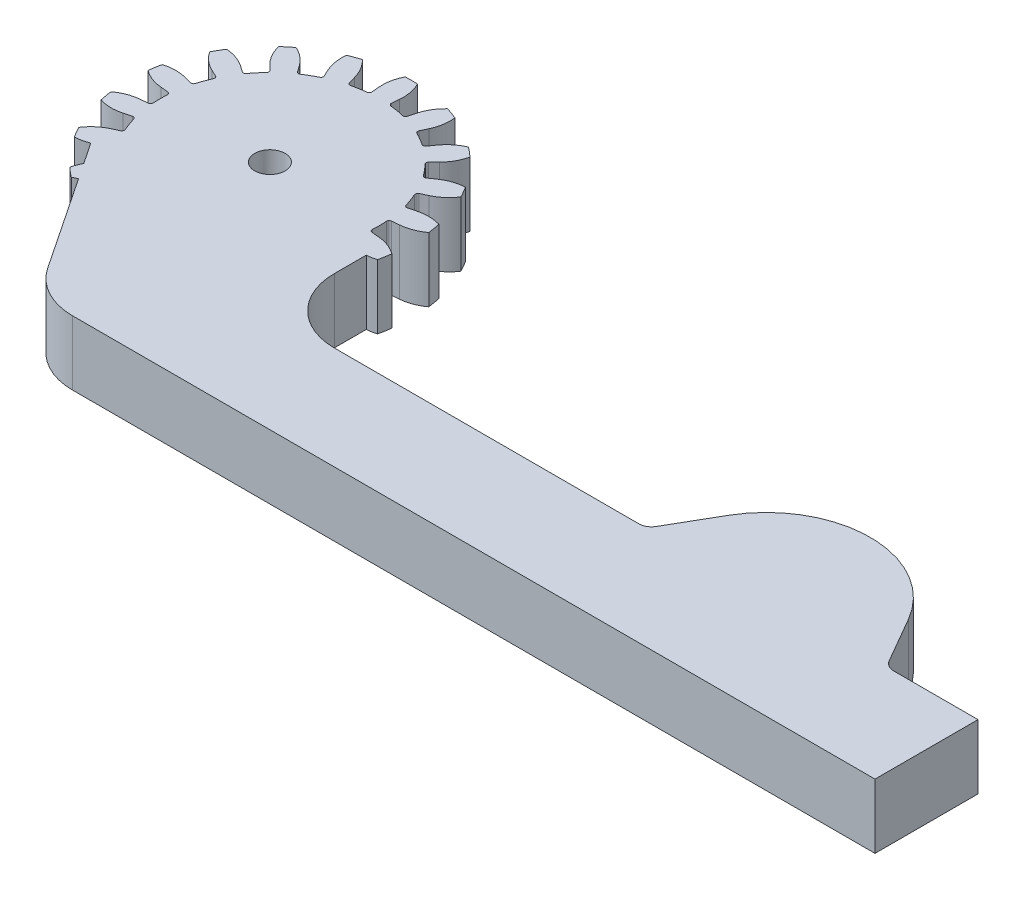
SolidWorks part; units mm, degrees
ref_plane "Front Plane" through (0, 0, 0) normal (0, 0, 1) x (1, 0, 0)
ref_plane "Top Plane" through (0, 0, 0) normal (0, 1, 0) x (1, 0, 0)
ref_plane "Right Plane" through (0, 0, 0) normal (1, 0, 0) x (0, 0, -1)
sketch "Sketch1" plane through (0, 0, 0) normal (0, 1, 0) x (1, 0, 0)
  line L0 (0, 0) -> (0, 13.97) construction
  line L1 (0, 0) -> (-0.6094, 13.9567) construction
  line L2 (0, 0) -> (-1.0297, 11.7695) construction
  line L3 (0, 0) -> (-1.88, 10.6623) construction
  line L4 (0, 0) -> (-1.88, 10.6623)
  line L5 (-0.9655, 11.0357) -> (-1.0297, 11.7695)
  line L6 (0, 0) -> (1.88, 10.6623)
  line L7 (0.9655, 11.0357) -> (1.0297, 11.7695)
  circle A0 centre (0, 0) radius 13.97 construction
  circle A1 centre (0, 0) radius 11.8144 construction
  circle A2 centre (0, 0) radius 10.8268 construction
  arc A3 (-1.88, 10.6623) -> (-1.1906, 10.7611) centre (0, 0) cw
  arc A4 (-1.0297, 11.7695) -> (-0.6094, 13.9567) centre (3.0252, 12.1242) cw
  arc A5 (-0.6094, 13.9567) -> (0.6094, 13.9567) centre (0, 0) cw
  arc A6 (1.88, 10.6623) -> (1.1906, 10.7611) centre (0, 0) ccw
  arc A7 (1.0297, 11.7695) -> (0.6094, 13.9567) centre (-3.0252, 12.1242) ccw
  arc A8 (-0.9655, 11.0357) -> (-1.1906, 10.7611) centre (-1.2185, 11.0135) cw
  arc A9 (1.1906, 10.7611) -> (0.9655, 11.0357) centre (1.2185, 11.0135) cw
  point P18 (-0.9436, 10.7856)
  point P21 (0.9436, 10.7856)
  dimension "D1" = 27.94
  dimension "D2" = 23.6289
  dimension "D3" = 3.1433
  dimension "D7" = 0.254
  dimension "D8" = 0.254
  dimension "D4" = 10
  dimension "D5" = 5
  dimension "D6" = 2.5
extrude "Boss-Extrude1" add sketch "Sketch1" along normal blind 6.35
pattern_circular "CirPattern1" count 18 over 360 about axis through (0, 0, 0) along (0, 1, 0) of "Boss-Extrude1"
sketch "Sketch2" plane through (0, 6.35, 0) normal (0, 1, 0) x (1, 0, 0)
  line L0 (57.15, -12.7) -> (57.15, 0) construction
  line L1 (19.05, -12.7) -> (49.0844, -12.7)
  line L2 (0, -12.7) -> (0, -22.86) construction
  line L3 (3.3942, -22.86) -> (57.15, -22.86)
  line L4 (57.15, -12.7) -> (57.15, -22.86) construction
  line L5 (57.37, -0.381) -> (69.2484, -20.955)
  line L6 (68.1485, -22.86) -> (57.15, -22.86)
  line L7 (56.93, -0.381) -> (50.1843, -12.065)
  line L8 (-1.8857, -20.0378) -> (-10.5598, -7.0556)
  line L9 (12.7, -3.175) -> (12.7, -6.35) construction
  line L10 (12.7, -3.175) -> (12.7, -6.35)
  line L11 (-10.5598, -7.0556) -> (0, 0)
  line L12 (74.2494, -12.7) -> (82.55, -12.7)
  line L13 (0, 0) -> (12.7, -3.175)
  line L14 (82.55, -12.7) -> (82.55, -22.86)
  line L15 (82.55, -22.86) -> (68.1485, -22.86)
  line L16 (73.1496, -12.065) -> (66.4038, -0.381)
  line L17 (66.4038, -0.381) -> (59.4576, -0.381)
  line L18 (50.1843, -12.065) -> (49.8177, -12.7)
  line L19 (49.8177, -12.7) -> (49.0844, -12.7)
  line L20 (49.8177, -12.7) -> (73.5162, -12.7)
  arc A0 (12.7, 0) -> (12.3208, -3.0802) centre (0, 0) ccw construction
  arc A1 (57.37, -0.381) -> (56.93, -0.381) centre (57.15, -0.508) ccw
  arc A2 (3.3942, -22.86) -> (-1.8857, -20.0378) centre (3.3942, -16.51) cw
  arc A3 (19.05, -12.7) -> (12.7, -6.35) centre (19.05, -6.35) cw
  arc A4 (49.0844, -12.7) -> (50.1843, -12.065) centre (49.0844, -11.43) ccw
  arc A5 (68.1485, -22.86) -> (69.2484, -20.955) centre (68.1485, -21.59) ccw
  arc A6 (70.5539, -7.5691) -> (52.78, -7.5691) centre (61.6669, -12.7) ccw
  arc A7 (74.2494, -12.7) -> (73.1496, -12.065) centre (74.2494, -11.43) cw
  dimension "D1" = 25.4
  dimension "D6" = 0.254
  dimension "D7" = 6.35
  dimension "D8" = 6.35
  dimension "D9" = 1.27
  dimension "D10" = 1.27
  dimension "D12" = 1.27
  dimension "D2" = 10.16
  dimension "D3" = 57.15
  dimension "D4" = 30
  dimension "D5" = 30
  dimension "D11" = 25.4
sketch "Sketch4" plane through (0, 6.35, 0) normal (0, 1, 0) x (1, 0, 0)
  circle A0 centre (0, 0) radius 1.5
  dimension "D1" = 3
extrude "Boss-Extrude3" add sketch "Sketch2" along normal blind 6.35 from surface at -6.35 starting at plane "Top Plane"
extrude "Cut-Extrude1" cut sketch "Sketch4" against normal blind 6.35
